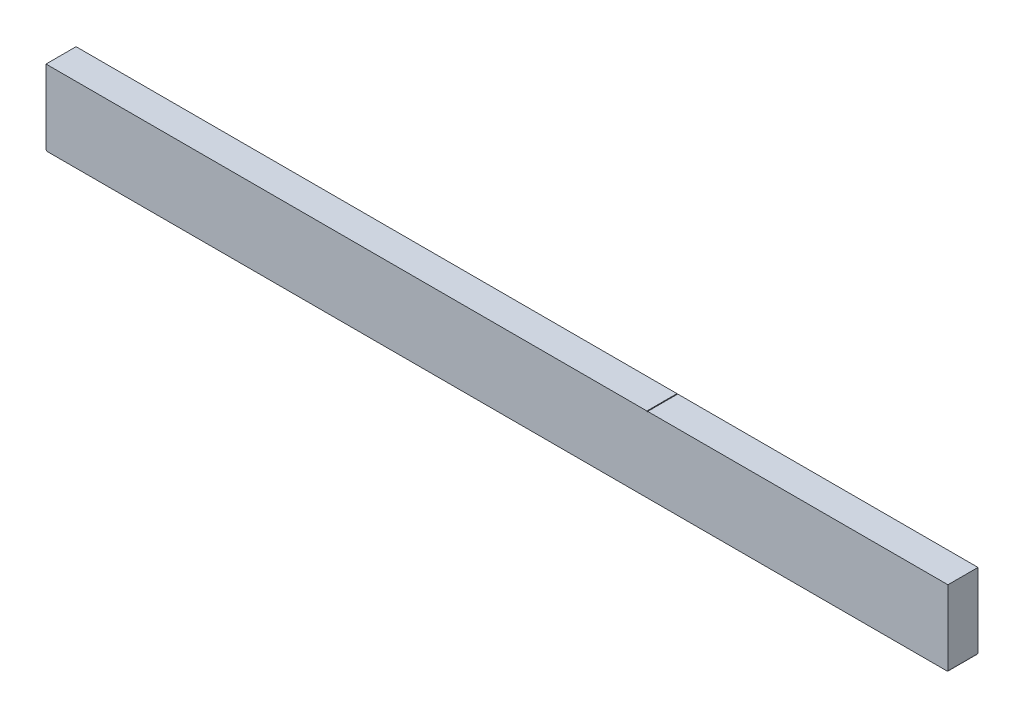
SolidWorks part; units mm, degrees
ref_plane "Front Plane" through (0, 0, 0) normal (0, 0, 1) x (1, 0, 0)
ref_plane "Top Plane" through (0, 0, 0) normal (0, 1, 0) x (1, 0, 0)
ref_plane "Right Plane" through (0, 0, 0) normal (1, 0, 0) x (0, 0, -1)
sketch "Sketch1" plane through (0, 0, 0) normal (1, 0, 0) x (0, 0, -1)
  line L1 (-100, -250) -> (100, -250)
  line L2 (-100, -250) -> (-100, 250)
  line L3 (-100, 250) -> (100, 250)
  line L4 (100, -250) -> (100, 250)
  line L5 (-100, -250) -> (100, 250) construction
  line L6 (-100, 250) -> (100, -250) construction
  point P0 (0, 0)
  dimension "D1" = 200
  dimension "D2" = 500
extrude "Boss-Extrude1" add sketch "Sketch1" along normal blind 6000
sketch "Sketch3" plane through (0, 0, 100) normal (0, 0, 1) x (1, 0, 0)
  line L0 (6000, 250) -> (0, 250) construction
  line L1 (-2.5, -255) -> (2.5, -255)
  line L2 (-2.5, -255) -> (-2.5, -245)
  line L3 (-2.5, -245) -> (2.5, -245)
  line L4 (2.5, -255) -> (2.5, -245)
  line L5 (-2.5, -255) -> (2.5, -245) construction
  line L6 (-2.5, -245) -> (2.5, -255) construction
  line L7 (5997.5, -255) -> (6002.5, -255)
  line L8 (5997.5, -255) -> (5997.5, -245)
  line L9 (5997.5, -245) -> (6002.5, -245)
  line L10 (6002.5, -255) -> (6002.5, -245)
  line L11 (5997.5, -255) -> (6002.5, -245) construction
  line L12 (5997.5, -245) -> (6002.5, -255) construction
  line L13 (3997.5, 245) -> (4002.5, 245)
  line L14 (3997.5, 245) -> (3997.5, 255)
  line L15 (3997.5, 255) -> (4002.5, 255)
  line L16 (4002.5, 245) -> (4002.5, 255)
  line L17 (3997.5, 245) -> (4002.5, 255) construction
  line L18 (3997.5, 255) -> (4002.5, 245) construction
  line L19 (6000, 250) -> (6000, -250) construction
  point P0 (0, -250)
  point P6 (6000, -250)
  point P12 (4000, 250)
  dimension "D1" = 10
  dimension "D2" = 5
  dimension "D3" = 5
  dimension "D4" = 10
  dimension "D5" = 10
  dimension "D6" = 2000
  dimension "D7" = 5
extrude "Cut-Extrude1" cut sketch "Sketch3" against normal through all
